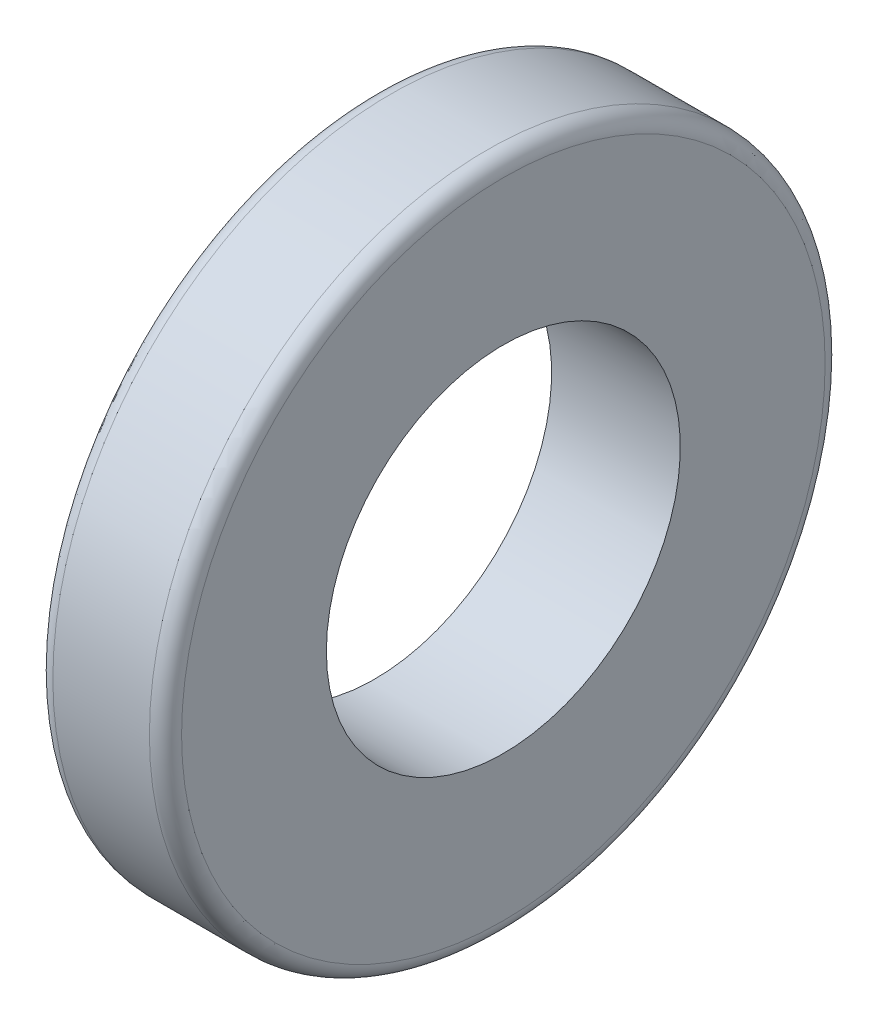
SolidWorks part; units mm, degrees
ref_plane "Front Plane" through (0, 0, 0) normal (0, 0, 1) x (1, 0, 0)
ref_plane "Top Plane" through (0, 0, 0) normal (0, 1, 0) x (1, 0, 0)
ref_plane "Right Plane" through (0, 0, 0) normal (1, 0, 0) x (0, 0, -1)
sketch "Sketch1" plane through (0, 0, 0) normal (0, 0, 1) x (1, 0, 0)
  line L0 (0, 0) -> (6, 0) construction
  line L2 (1, 10.5) -> (5, 10.5)
  line L3 (1, 10.5) -> (1, 5.5)
  line L4 (1, 5.5) -> (5, 5.5)
  line L5 (5, 10.5) -> (5, 5.5)
  line L6 (1, 10.5) -> (5, 5.5) construction
  line L7 (1, 5.5) -> (5, 10.5) construction
  point P3 (3, 8)
  point P10 (3, 0)
  dimension "D1" = 10.5
  dimension "D2" = 4
  dimension "D3" = 5
  dimension "D4" = 6
revolve "Revolve1" add sketch "Sketch1" angle 360 about L0
fillet "Fillet1" radius 0.5 2 edges at (1, 0, 10.5) (5, 0, 10.5)
